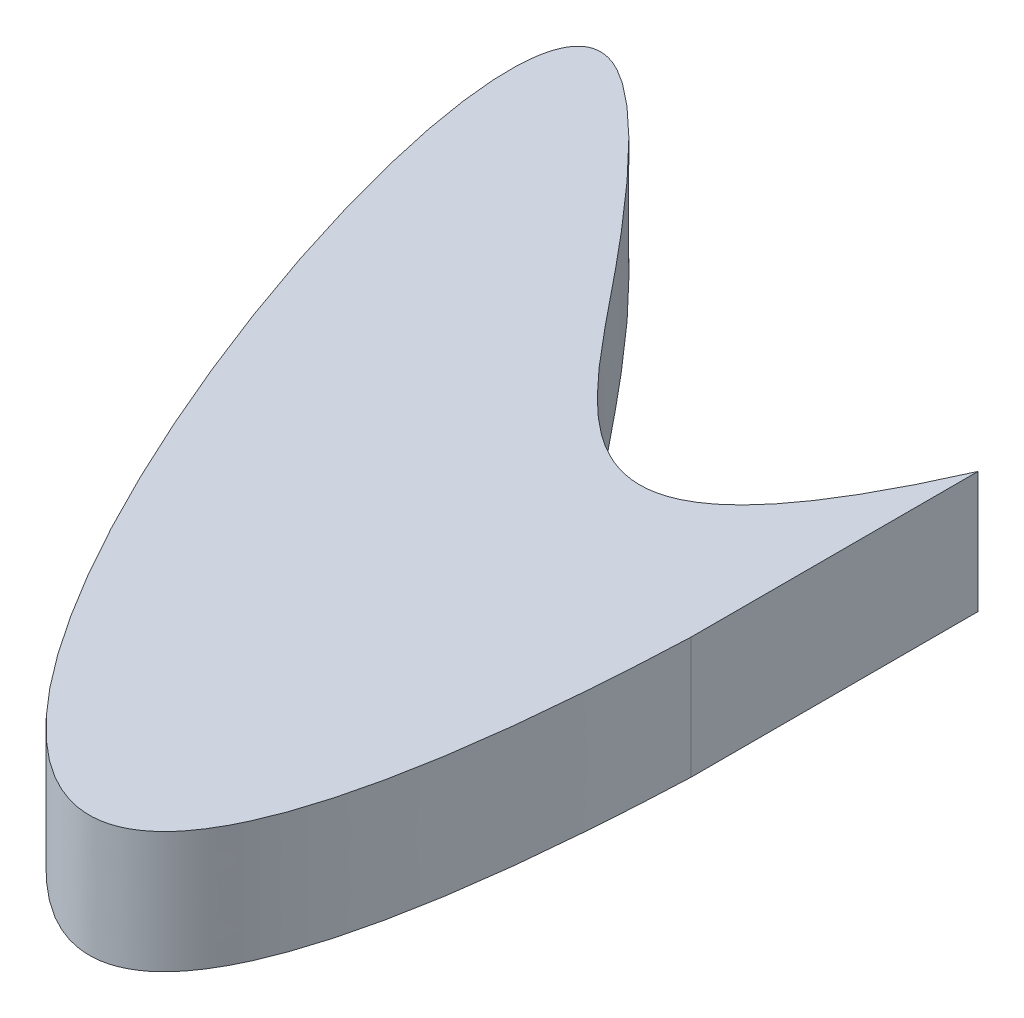
SolidWorks part; units mm, degrees
ref_plane "Front Plane" through (0, 0, 0) normal (0, 0, 1) x (1, 0, 0)
ref_plane "Top Plane" through (0, 0, 0) normal (0, 1, 0) x (1, 0, 0)
ref_plane "Right Plane" through (0, 0, 0) normal (1, 0, 0) x (0, 0, -1)
sketch "Sketch2" plane through (0, 0, 0) normal (0, 1, 0) x (1, 0, 0)
  line L0 (0, 4.1858) -> (0, -10.8142)
  spline S0 degree 3 poles (0, -10.8142) (-2.6609, -77.8297) (-47.0691, 35.8621) (-14.5138, -0.363) (-7.0611, -11.8771) (0, 4.1858) knots 0 0 0 0 0.65497 0.773194 1 1 1 1
  point P4 (-5.0787, 19.9724)
  point P6 (-14.1201, 1.7751)
  point P8 (-28.4262, 19.858)
  point P10 (-21.4448, -12.9887)
  point P11 (-27.9684, 13.1055)
  point P12 (-11.2454, -1.8118)
  point P13 (-18.4925, 3.686)
  point P14 (-9.871, -4.9355)
  point P15 (0, 0)
  point P16 (0, 16.9306)
  point P17 (0, 4.1858)
  point P18 (-11.3704, -33.0491)
  dimension "D1" = 15
extrude "Boss-Extrude1" add sketch "Sketch2" along normal blind 6.35
